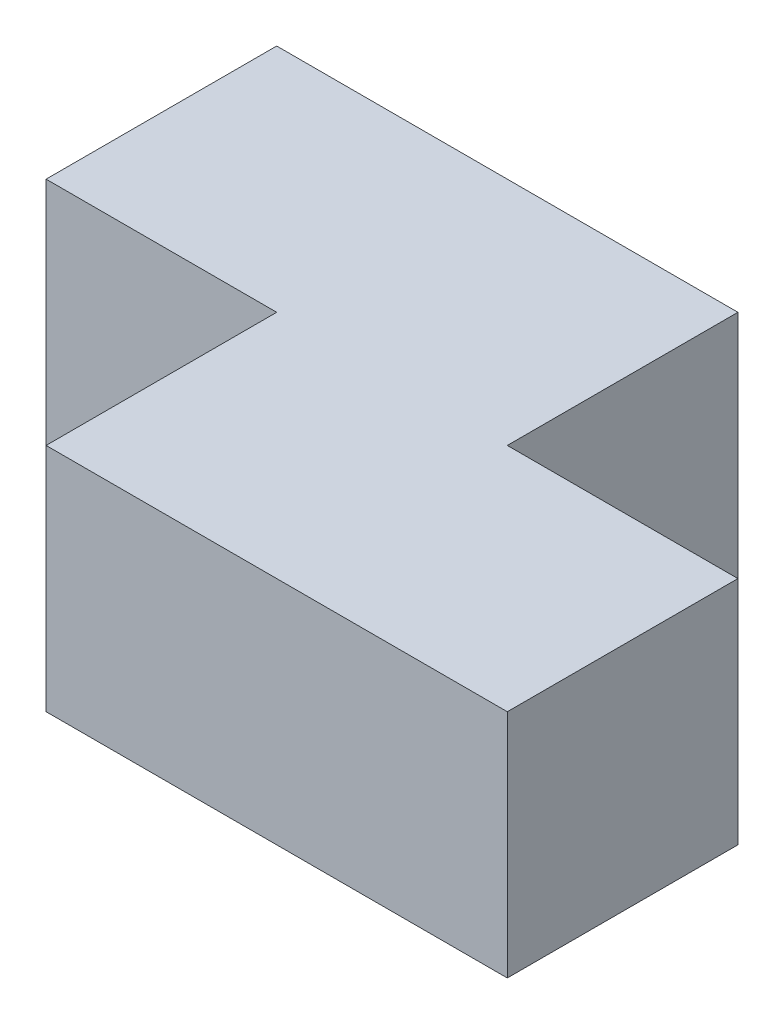
SolidWorks part; units mm, degrees
ref_plane "Front Plane" through (0, 0, 0) normal (0, 0, 1) x (1, 0, 0)
ref_plane "Top Plane" through (0, 0, 0) normal (0, 1, 0) x (1, 0, 0)
ref_plane "Right Plane" through (0, 0, 0) normal (1, 0, 0) x (0, 0, -1)
sketch "Sketch1" plane through (0, 0, 0) normal (0, 1, 0) x (1, 0, 0)
  line L1 (-38.1, -25.4) -> (38.1, -25.4)
  line L2 (-38.1, -25.4) -> (-38.1, 25.4)
  line L3 (-38.1, 25.4) -> (38.1, 25.4)
  line L4 (38.1, -25.4) -> (38.1, 25.4)
  line L5 (-38.1, -25.4) -> (38.1, 25.4) construction
  line L6 (-38.1, 25.4) -> (38.1, -25.4) construction
  point P0 (0, 0)
  dimension "D1" = 76.2
  dimension "D2" = 50.8
extrude "Boss-Extrude1" add sketch "Sketch1" along normal blind 25.4
sketch "Sketch2" plane through (0, 25.4, 0) normal (0, 1, 0) x (1, 0, 0)
  line L1 (-38.1, -25.4) -> (-12.7, -25.4)
  line L2 (-38.1, -25.4) -> (-38.1, 0)
  line L3 (-38.1, 0) -> (-12.7, 0)
  line L4 (-12.7, -25.4) -> (-12.7, 0)
  dimension "D1" = 25.4
  dimension "D2" = 25.4
extrude "Cut-Extrude1" cut sketch "Sketch2" against normal through all
sketch "Sketch3" plane through (0, 25.4, 0) normal (0, 1, 0) x (1, 0, 0)
  line L0 (38.1, 25.4) -> (-38.1, 25.4) construction
  line L1 (38.1, 25.4) -> (12.7, 25.4)
  line L2 (38.1, 25.4) -> (38.1, 0)
  line L3 (38.1, 0) -> (12.7, 0)
  line L4 (12.7, 25.4) -> (12.7, 0)
  dimension "D1" = 25.4
  dimension "D2" = 25.4
extrude "Cut-Extrude2" cut sketch "Sketch3" against normal through all
